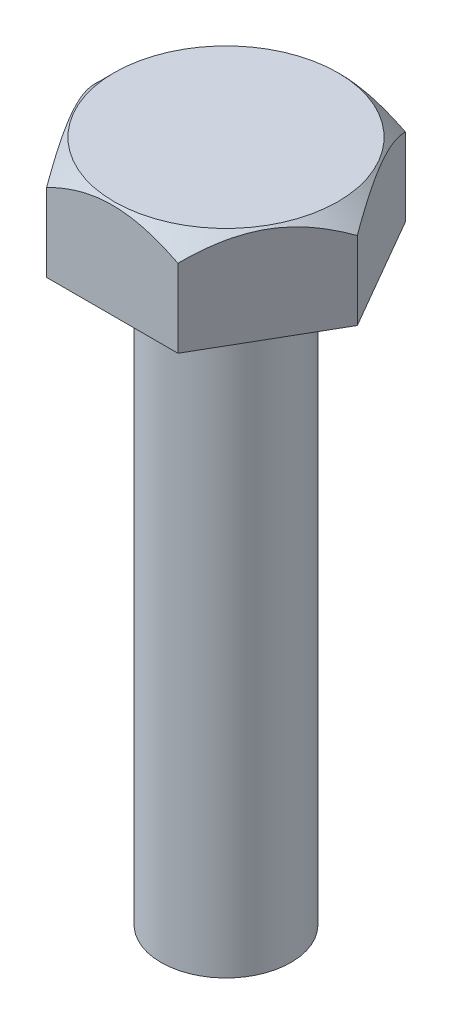
SolidWorks part; units mm, degrees
ref_plane "Front Plane" through (0, 0, 0) normal (0, 0, 1) x (1, 0, 0)
ref_plane "Top Plane" through (0, 0, 0) normal (0, 1, 0) x (1, 0, 0)
ref_plane "Right Plane" through (0, 0, 0) normal (1, 0, 0) x (0, 0, -1)
sketch "Sketch1" plane through (0, 0, 0) normal (0, 1, 0) x (1, 0, 0)
  circle A0 centre (0, 0) radius 10
  dimension "D1" = 20
extrude "Boss-Extrude1" add sketch "Sketch1" along normal blind 105
sketch "Sketch2" plane through (0, 105, 0) normal (0, 1, 0) x (1, 0, 0)
  line L1 (20.2073, 0) -> (10.1036, 17.5)
  line L2 (10.1036, 17.5) -> (-10.1036, 17.5)
  line L3 (-10.1036, 17.5) -> (-20.2073, 0)
  line L4 (-20.2073, 0) -> (-10.1036, -17.5)
  line L5 (-10.1036, -17.5) -> (10.1036, -17.5)
  line L6 (10.1036, -17.5) -> (20.2073, 0)
  circle A0 centre (0, 0) radius 17.5 construction
  dimension "D1" = 35
extrude "Boss-Extrude2" add sketch "Sketch2" against normal blind 15
sketch "Sketch3" plane through (0, 0, 0) normal (0, 0, 1) x (1, 0, 0)
  line L0 (20.2073, 90) -> (20.2073, 105) construction
  line L1 (10.1036, 105) -> (20.2073, 105) construction
  line L2 (20.2073, 105) -> (20.2073, 102)
  line L3 (20.2073, 105) -> (17.2073, 105)
  line L4 (17.2073, 105) -> (20.2073, 102)
  line L5 (0, 0) -> (0, 52.2797) construction
revolve "Cut-Revolve1" cut sketch "Sketch3" angle 360 about L5
